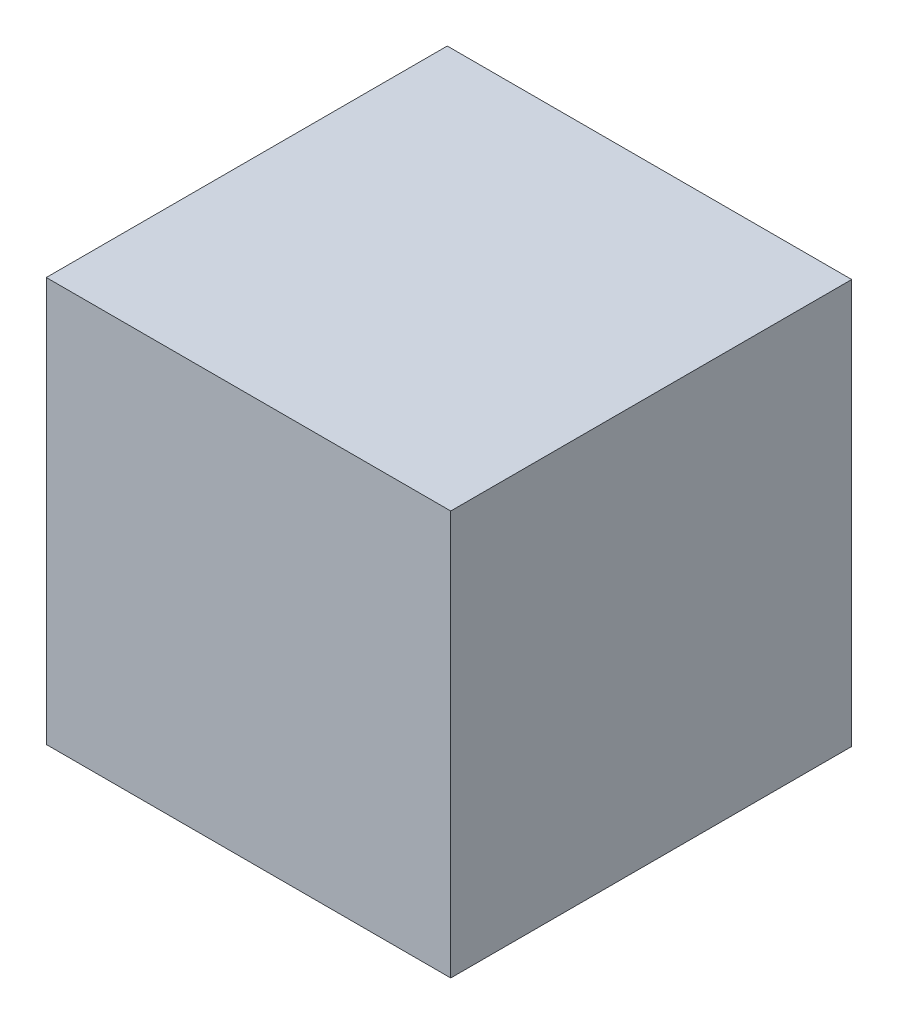
SolidWorks part; units mm, degrees
ref_plane "Plan de face" through (0, 0, 0) normal (0, 0, 1) x (1, 0, 0)
ref_plane "Plan de dessus" through (0, 0, 0) normal (0, 1, 0) x (1, 0, 0)
ref_plane "Plan de droite" through (0, 0, 0) normal (1, 0, 0) x (0, 0, -1)
sketch "Esquisse1" plane through (0, 0, 0) normal (0, 0, 1) x (1, 0, 0)
  line L0 (-66.2829, 51.5773) -> (49.7171, 51.5773)
  line L1 (-66.2829, 51.5773) -> (-66.2829, -64.4227)
  line L2 (49.7171, 51.5773) -> (49.7171, -64.4227)
  line L3 (-66.2829, -64.4227) -> (49.7171, -64.4227)
  dimension "D1" = 116
  dimension "D2" = 116
extrude "Boss.-Extru.1" add sketch "Esquisse1" along normal blind 115
